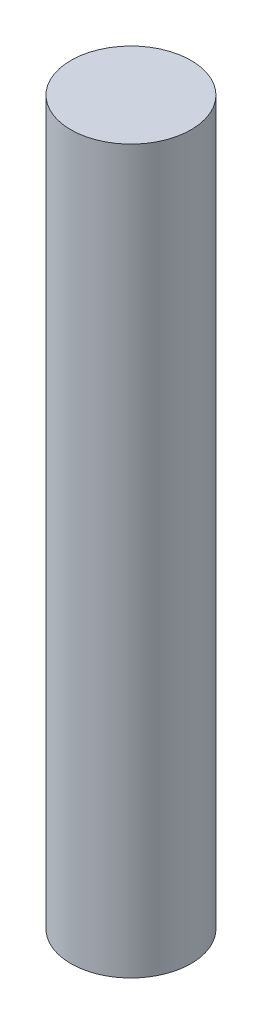
SolidWorks part; units mm, degrees
ref_plane "Front Plane" through (0, 0, 0) normal (0, 0, 1) x (1, 0, 0)
ref_plane "Top Plane" through (0, 0, 0) normal (0, 1, 0) x (1, 0, 0)
ref_plane "Right Plane" through (0, 0, 0) normal (1, 0, 0) x (0, 0, -1)
sketch "Sketch1" plane through (0, 0, 0) normal (0, 1, 0) x (1, 0, 0)
  circle A0 centre (0, 0) radius 6.34
  dimension "D1" = 12.68
extrude "Boss-Extrude1" add sketch "Sketch1" along normal blind 76.17
